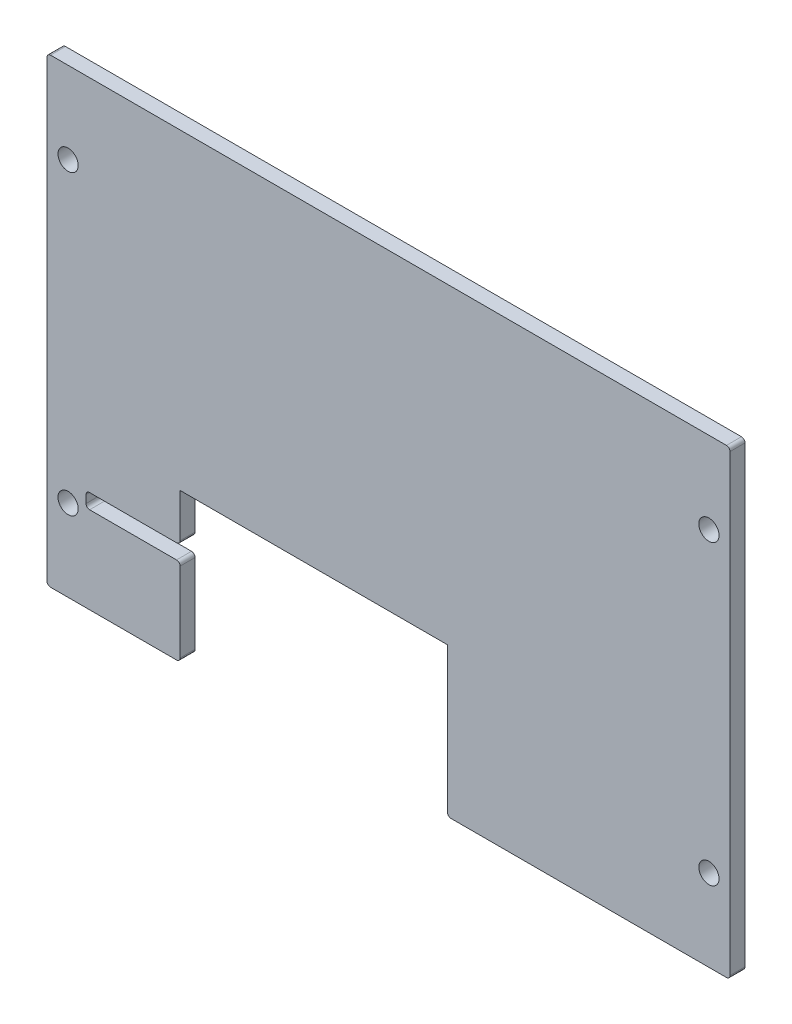
SolidWorks part; units mm, degrees
ref_plane "Front Plane" through (0, 0, 0) normal (0, 0, 1) x (1, 0, 0)
ref_plane "Top Plane" through (0, 0, 0) normal (0, 1, 0) x (1, 0, 0)
ref_plane "Right Plane" through (0, 0, 0) normal (1, 0, 0) x (0, 0, -1)
sketch "Sketch1" plane through (0, 0, 0) normal (0, 0, 1) x (1, 0, 0)
  line L1 (0, 98.425) -> (145.8854, 98.425)
  line L2 (0, 98.425) -> (0, 0)
  line L3 (0, 0) -> (145.8854, 0)
  line L4 (145.8854, 98.425) -> (145.8854, 0)
  dimension "D1" = 98.425
  dimension "D2" = 145.8854
extrude "Boss-Extrude1" add sketch "Sketch1" along normal blind 3.2004
sketch "Sketch4" plane through (0, 0, 3.2004) normal (0, 0, 1) x (1, 0, 0)
  line L0 (0, 98.425) -> (0, 0) construction
  line L1 (28.4328, 31.75) -> (85.5328, 31.75)
  line L2 (28.4328, 31.75) -> (28.4328, 0)
  line L3 (28.4328, 0) -> (85.5328, 0)
  line L4 (85.5328, 31.75) -> (85.5328, 0)
  line L5 (0, 0) -> (145.8854, 0) construction
  dimension "D1" = 28.4328
  dimension "D2" = 57.1
  dimension "D3" = 31.75
extrude "Cut-Extrude1" cut sketch "Sketch4" against normal up to surface (3.2004 mm away) up to face at (72.9427, 49.2125, 0)
sketch "Sketch5" plane through (0, 0, 3.2004) normal (0, 0, 1) x (1, 0, 0)
  line L0 (0, 49.2125) -> (4.5085, 49.2125) construction
  line L1 (4.5085, 17.4625) -> (4.5085, 80.9625) construction
  line L2 (141.3769, 49.2125) -> (145.8854, 49.2125) construction
  line L3 (141.3769, 17.4625) -> (141.3769, 80.9625) construction
  line L4 (0, 98.425) -> (0, 0) construction
  line L5 (145.8854, 0) -> (145.8854, 98.425) construction
  circle A0 centre (141.3769, 80.9625) radius 2.159
  circle A1 centre (141.3769, 17.4625) radius 2.159
  circle A2 centre (4.5085, 17.4625) radius 2.159
  circle A3 centre (4.5085, 80.9625) radius 2.159
  dimension "D3" = 4.318
  dimension "D1" = 4.5085
  dimension "D2" = 63.5
extrude "Cut-Extrude2" cut sketch "Sketch5" against normal up to surface (3.2004 mm away) up to face at (64.9627, 32.5437, 0)
sketch "Sketch7" plane through (0, 0, 0) normal (0, 0, -1) x (-1, 0, 0)
  line L1 (-28.4328, 18.5115) -> (-8.3399, 18.5115)
  line L2 (-28.4328, 18.5115) -> (-28.4328, 21.6865)
  line L3 (-28.4328, 21.6865) -> (-8.3399, 21.6865)
  line L4 (-8.3399, 18.5115) -> (-8.3399, 21.6865)
  line L5 (-28.4328, 0) -> (-28.4328, 31.75) construction
  line L6 (0, 0) -> (-28.4328, 0) construction
  line L7 (0, 0) -> (-28.4328, 0) construction
  point P8 (-28.4328, 20.099)
  dimension "D1" = 3.175
  dimension "D2" = 20.099
extrude "Cut-Extrude4" cut sketch "Sketch7" against normal up to surface (3.2004 mm away) up to face at (6.6675, 80.9625, 3.2004)
fillet "Fillet1" radius 0.762 10 edges at (145.8854, 0, 1.6002) (85.5328, 0, 1.6002) (28.4328, 0, 1.6002) (0, 0, 1.6002) (145.8854, 98.425, 1.6002) (0, 98.425, 1.6002) (28.4328, 18.5115, 1.6002) (28.4328, 21.6865, 1.6002) (8.3399, 21.6865, 1.6002) (8.3399, 18.5115, 1.6002)
